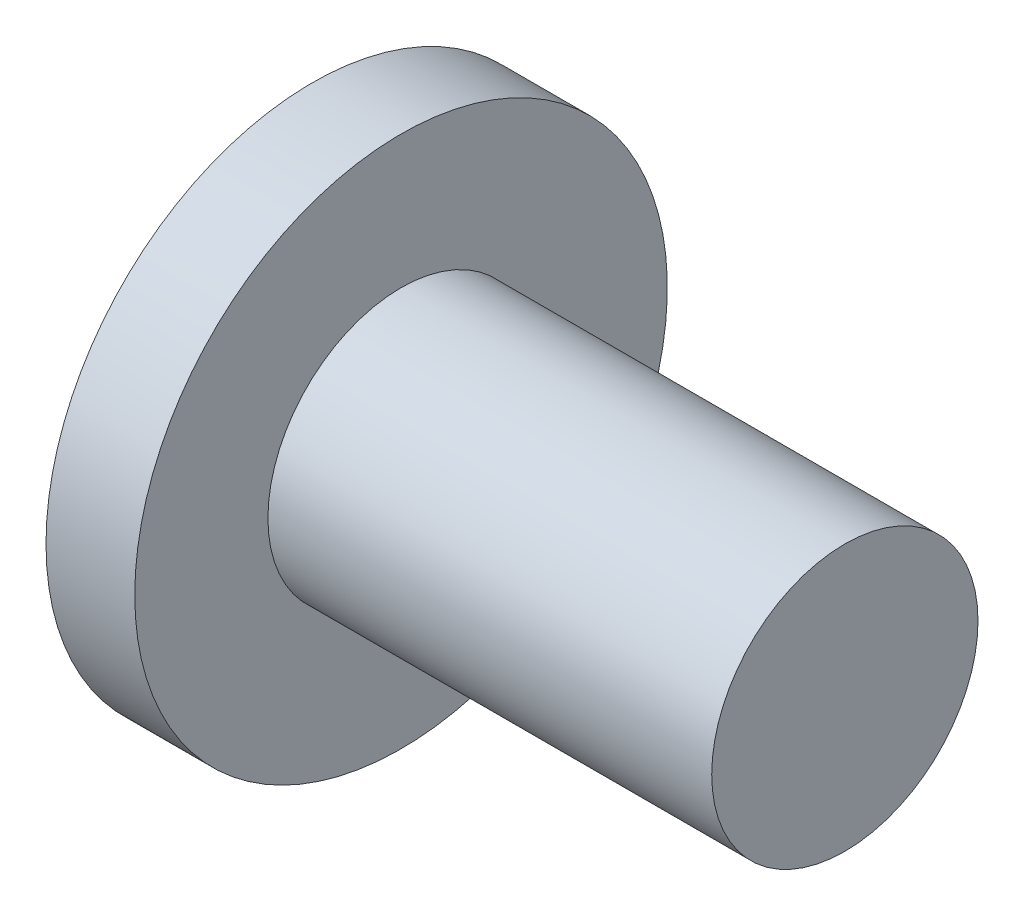
SolidWorks part; units mm, degrees
ref_plane "Ön Düzlem" through (0, 0, 0) normal (0, 0, 1) x (1, 0, 0)
ref_plane "Üst Düzlem" through (0, 0, 0) normal (0, 1, 0) x (1, 0, 0)
ref_plane "Sağ Düzlem" through (0, 0, 0) normal (1, 0, 0) x (0, 0, -1)
sketch "Çizim1" plane through (0, 0, 0) normal (0, 0, 1) x (1, 0, 0)
  line L0 (-21.4703, 0) -> (21.4703, 0) construction
  line L1 (0, 0) -> (0, 6)
  line L2 (0, 6) -> (2, 6)
  line L3 (2, 6) -> (2, 3)
  line L4 (2, 3) -> (12, 3)
  line L5 (12, 3) -> (12, 0)
  line L6 (0, 0) -> (12, 0)
  point P4 (0, 0)
  dimension "D1" = 6
  dimension "D2" = 2
  dimension "D3" = 10
  dimension "D4" = 3
revolve "Döndür1" add sketch "Çizim1" angle 360 about L0
